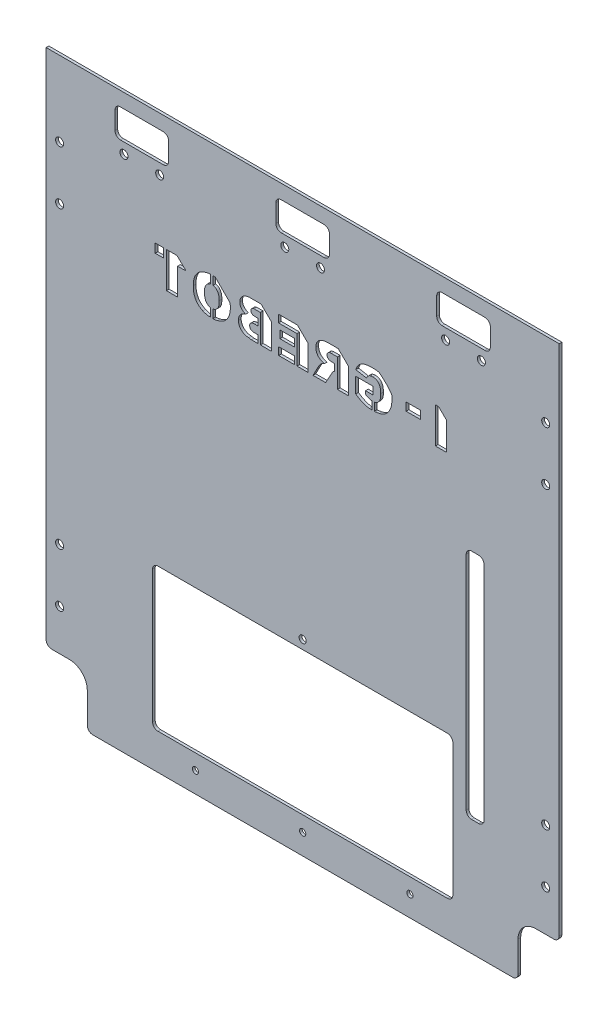
SolidWorks part; units mm, degrees
material "1023 Tôle d'acier au carbone (SS)"
ref_plane "Front" through (0, 0, 0) normal (0, 0, 1) x (1, 0, 0)
ref_plane "Top" through (0, 0, 0) normal (0, 1, 0) x (1, 0, 0)
ref_plane "Right" through (0, 0, 0) normal (1, 0, 0) x (0, 0, -1)
sketch "Esquisse1" plane through (0, 0, 0) normal (0, 0, 1) x (1, 0, 0)
  line L1 (0, 0) -> (287, 0)
  line L2 (0, 0) -> (0, 320)
  line L3 (0, 320) -> (287, 320)
  line L4 (287, 0) -> (287, 320)
  dimension "D1" = 287
  dimension "D2" = 320
extrude "Boss.-Extru.1" add sketch "Esquisse1" along normal blind 1.5
sketch "Esquisse2" plane through (0, 0, 1.5) normal (0, 0, 1) x (1, 0, 0)
  line L0 (143.5, 0) -> (143.5, 172.6222) construction
  line L1 (287, 0) -> (264, 0)
  line L2 (287, 0) -> (287, 30)
  line L3 (287, 30) -> (264, 30)
  line L4 (264, 0) -> (264, 30)
  line L5 (0, 0) -> (287, 0) construction
  line L6 (23, 0) -> (23, 30)
  line L7 (0, 30) -> (23, 30)
  line L8 (0, 0) -> (0, 30)
  line L9 (0, 0) -> (23, 0)
  dimension "D1" = 23
  dimension "D2" = 30
extrude "Enlèv. mat.-Extru.1" cut sketch "Esquisse2" against normal through all both and the other way through all
fillet "Congé1" radius 10 2 edges at (23, 30, 0.75) (264, 30, 0.75)
fillet "Congé2" radius 3 4 edges at (264, 0, 0.75) (287, 30, 0.75) (23, 0, 0.75) (0, 30, 0.75)
sketch "Esquisse3" plane through (0, 0, 1.5) normal (0, 0, 1) x (1, 0, 0)
  line L0 (26, 0) -> (261, 0) construction
  line L1 (235, 195) -> (245, 195)
  line L2 (235, 195) -> (235, 65)
  line L3 (235, 65) -> (245, 65)
  line L4 (245, 195) -> (245, 65)
  dimension "D1" = 10
  dimension "D2" = 235
  dimension "D3" = 65
  dimension "D4" = 130
extrude "Enlèv. mat.-Extru.2" cut sketch "Esquisse3" against normal through all both and the other way through all
sketch "Esquisse4" plane through (0, 0, 1.5) normal (0, 0, 1) x (1, 0, 0)
  line L0 (26, 0) -> (261, 0) construction
  line L1 (59.5, 20) -> (227.5, 20)
  line L2 (59.5, 20) -> (59.5, 100)
  line L3 (59.5, 100) -> (227.5, 100)
  line L4 (227.5, 20) -> (227.5, 100)
  line L5 (143.5, 20) -> (143.5, 0) construction
  dimension "D1" = 80
  dimension "D2" = 20
  dimension "D3" = 168
extrude "Enlèv. mat.-Extru.3" cut sketch "Esquisse4" against normal through all both and the other way through all
fillet "Congé3" radius 3 8 edges at (235, 195, 0.75) (245, 195, 0.75) (245, 65, 0.75) (235, 65, 0.75) (227.5, 20, 0.75) (227.5, 100, 0.75) (59.5, 100, 0.75) (59.5, 20, 0.75)
sketch "Esquisse5" plane through (0, 0, 1.5) normal (0, 0, 1) x (1, 0, 0)
  line L0 (143.5, 0) -> (143.5, 105) construction
  line L1 (26, 0) -> (261, 0) construction
  line L2 (143.5, 11.5) -> (83.5, 11.5) construction
  line L3 (224.5, 20) -> (62.5, 20) construction
  circle A0 centre (143.5, 105) radius 2
  circle A1 centre (83.5, 11.5) radius 1.75
  circle A2 centre (143.5, 11.5) radius 1.75
  circle A3 centre (203.5, 11.5) radius 1.75
  point P10 (145.0841, 11.5)
  dimension "D1" = 4
  dimension "D4" = 3.5
  dimension "D6" = 60
  dimension "D2" = 105
  dimension "D5" = 8.5
extrude "Enlèv. mat.-Extru.4" cut sketch "Esquisse5" against normal through all both and the other way through all
sketch "Esquisse6" plane through (0, 0, 1.5) normal (0, 0, 1) x (1, 0, 0)
  line L0 (279.5, 308.1366) -> (279.5, -83.1051) construction
  line L1 (43.5, 290) -> (63.5, 290) construction
  line L2 (143.5, 0) -> (143.5, 67.282) construction
  line L3 (26, 0) -> (261, 0) construction
  line L4 (279.5, 165.5) -> (143.5, 165.5) construction
  line L5 (143.5, 320) -> (143.5, 263.6078) construction
  line L6 (287, 320) -> (0, 320) construction
  line L7 (243.5, 290) -> (223.5, 290) construction
  circle A0 centre (279.5, 83) radius 2.25
  circle A1 centre (279.5, 53) radius 2.25
  circle A2 centre (279.5, 278) radius 2.25
  circle A3 centre (279.5, 248) radius 2.25
  circle A4 centre (7.5, 248) radius 2.25
  circle A5 centre (7.5, 278) radius 2.25
  circle A6 centre (7.5, 53) radius 2.25
  circle A7 centre (7.5, 83) radius 2.25
  circle A8 centre (133.5, 290) radius 2.25
  circle A9 centre (153.5, 290) radius 2.25
  circle A10 centre (43.5, 290) radius 2.25
  circle A11 centre (63.5, 290) radius 2.25
  circle A12 centre (223.5, 290) radius 2.25
  circle A13 centre (243.5, 290) radius 2.25
  point P36 (53.5, 290)
  dimension "D2" = 4.5
  dimension "D3" = 30
  dimension "D4" = 53
  dimension "D5" = 195
  dimension "D8" = 20
  dimension "D1" = 136
  dimension "D6" = 20
  dimension "D7" = 30
  dimension "D9" = 90
  dimension "D10" = 30
extrude "Enlèv. mat.-Extru.5" cut sketch "Esquisse6" against normal through all both and the other way through all
sketch "Esquisse7" plane through (0, 0, 1.5) normal (0, 0, 1) x (1, 0, 0)
  line L0 (133.5, 290) -> (153.5, 290) construction
  line L1 (143.5, 290) -> (143.5, 312) construction
  line L2 (158.5, 312) -> (128.5, 312)
  line L3 (128.5, 312) -> (128.5, 296)
  line L4 (128.5, 296) -> (158.5, 296)
  line L5 (158.5, 312) -> (158.5, 296)
  line L6 (43.5, 290) -> (63.5, 290) construction
  line L7 (53.5, 290) -> (53.5, 312) construction
  line L8 (68.5, 312) -> (38.5, 312)
  line L9 (38.5, 312) -> (38.5, 296)
  line L10 (38.5, 296) -> (68.5, 296)
  line L11 (68.5, 312) -> (68.5, 296)
  line L12 (233.5, 290) -> (233.5, 312) construction
  line L13 (243.5, 290) -> (223.5, 290) construction
  line L14 (218.5, 312) -> (218.5, 296)
  line L15 (248.5, 296) -> (218.5, 296)
  line L16 (248.5, 312) -> (248.5, 296)
  line L17 (218.5, 312) -> (248.5, 312)
  point P10 (143.5, 296)
  point P21 (53.5, 296)
  point P30 (233.5, 296)
  dimension "D1" = 22
  dimension "D2" = 16
  dimension "D3" = 30
  dimension "D4" = 30
  dimension "D5" = 22
  dimension "D6" = 16
extrude "Enlèv. mat.-Extru.6" cut sketch "Esquisse7" against normal through all both and the other way through all
fillet "Congé4" radius 3 12 edges at (218.5, 296, 0.75) (248.5, 296, 0.75) (248.5, 312, 0.75) (218.5, 312, 0.75) (128.5, 312, 0.75) (158.5, 312, 0.75) (128.5, 296, 0.75) (158.5, 296, 0.75) (68.5, 296, 0.75) (68.5, 312, 0.75) (38.5, 312, 0.75) (38.5, 296, 0.75)
sketch "Esquisse8" plane through (0, 0, 0) normal (0, 0, 1) x (1, 0, 0)
  line L0 (224.3085, 235.821) -> (62.6915, 235.821) construction
  line L1 (62.6915, 235.821) -> (62.6915, 270.892) construction
  line L3 (143.5, 245.5) -> (143.5, 100) construction
  line L4 (62.5, 100) -> (224.5, 100) construction
  line L5 (240, 195) -> (240, 296) construction
  line L6 (238, 195) -> (242, 195) construction
  line L7 (245.5, 296) -> (221.5, 296) construction
  line L8 (240, 245.5) -> (225.9949, 245.5) construction
  line L9 (143.5, 245.5) -> (143.5, 235.821) construction
  line L10 (201.4031, 248.9675) -> (209.4031, 248.9675)
  line L11 (201.4031, 248.9675) -> (201.4031, 244.4675)
  line L12 (201.4031, 244.4675) -> (209.4031, 244.4675)
  line L13 (209.4031, 248.9675) -> (209.4031, 244.4675)
  text T1 "I  GREBOT" font "CF StencilOrama" height 20
  point P19 (0, 0)
  point P20 (80.9491, 243.2996)
  point P21 (79.5097, 242.5319)
  point P23 (87.8583, 243.9713)
  point P24 (219.0336, 235.805)
  point P25 (217.0033, 236.8202)
  point P26 (205.6673, 244.9721)
  point P27 (205.795, 244.4152)
  point P28 (0, 0)
  point P29 (0, 0)
  point P30 (221.6555, 236.4332)
  point P31 (225.9949, 235.6169)
  point P32 (224.1044, 235.821)
  point P33 (224.3085, 235.821)
  point P34 (209.4031, 244.4675)
  dimension "D1" = 4.5
  dimension "D2" = 8
extrude "Enlèv. mat.-Extru.9" cut sketch "Esquisse8" along normal through all both and the other way through all
